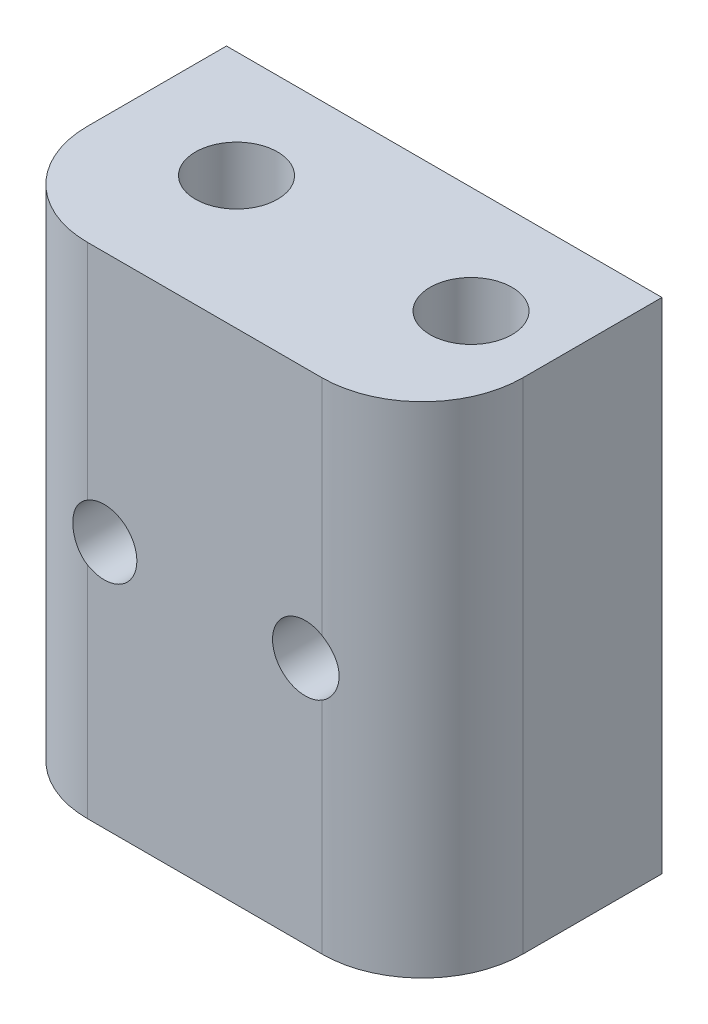
SolidWorks part; units mm, degrees
ref_plane "Front Plane" through (0, 0, 0) normal (0, 0, 1) x (1, 0, 0)
ref_plane "Top Plane" through (0, 0, 0) normal (0, 1, 0) x (1, 0, 0)
ref_plane "Right Plane" through (0, 0, 0) normal (1, 0, 0) x (0, 0, -1)
sketch "Sketch1" plane through (0, 0, 0) normal (0, 0, 1) x (1, 0, 0)
  line L1 (-13.1453, 13.6204) -> (12.8547, 13.6204)
  line L2 (-13.1453, 13.6204) -> (-13.1453, -16.1796)
  line L3 (-13.1453, -16.1796) -> (12.8547, -16.1796)
  line L4 (12.8547, 13.6204) -> (12.8547, -16.1796)
  dimension "D1" = 26
  dimension "D2" = 29.8
extrude "Extrude1" add sketch "Sketch1" along normal blind 14.3
sketch "Sketch2" plane through (0, 0, 14.3) normal (0, 0, 1) x (1, 0, 0)
  line L0 (-6.1453, -1.3796) -> (5.8547, -1.3796) construction
  line L1 (-0.1453, 13.6204) -> (-0.1453, -16.1796) construction
  line L2 (12.8547, 13.6204) -> (-13.1453, 13.6204) construction
  line L3 (-13.1453, -16.1796) -> (12.8547, -16.1796) construction
  circle A0 centre (-6.1453, -1.3796) radius 1.95
  circle A1 centre (5.8547, -1.3796) radius 1.95
  point P4 (-0.1453, -1.3796)
  dimension "D1" = 3.9
  dimension "D2" = 12
  dimension "D3" = 15
fillet "Fillet1" radius 6 2 edges at (12.8547, -1.2796, 14.3) (-13.1453, -1.2796, 14.3)
sketch "Sketch3" plane through (0, 13.6204, 0) normal (0, 1, 0) x (-1, 0, 0)
  line L0 (13.1453, 8.3) -> (13.1453, 0) construction
  line L1 (-6.8547, 14.3) -> (7.1453, 14.3) construction
  circle A0 centre (-7.8547, 6.4) radius 2.45
  circle A1 centre (6.1453, 6.4) radius 2.45
  dimension "D1" = 4.9
  dimension "D2" = 14
  dimension "D3" = 7
  dimension "D4" = 7.9
extrude "Cut-Extrude1" cut sketch "Sketch3" against normal through all
extrude "Extrude2" cut sketch "Sketch2" against normal through all
